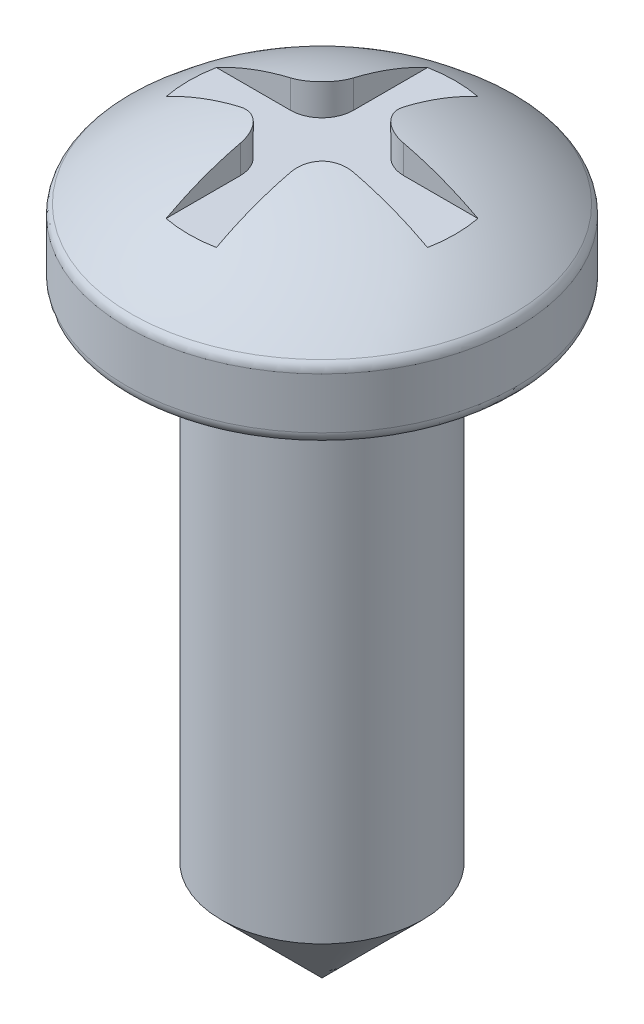
SolidWorks part; units mm, degrees
material "acero"
ref_plane "Alzado" through (0, 0, 0) normal (0, 0, 1) x (1, 0, 0)
ref_plane "Planta" through (0, 0, 0) normal (0, 1, 0) x (1, 0, 0)
ref_plane "Vista lateral" through (0, 0, 0) normal (1, 0, 0) x (0, 0, -1)
sketch "Croquis1" plane through (0, 0, 0) normal (0, 0, 1) x (1, 0, 0)
  line L0 (0, 0) -> (0, 11.9) construction
  line L1 (0, 0) -> (0, 11.9)
  line L2 (3.1, 9.7) -> (3.1, 10.5107)
  line L3 (2.9, 9.5) -> (1.6, 9.5)
  line L4 (1.6, 9.5) -> (1.6, 1.6)
  line L5 (1.6, 1.6) -> (0, 0)
  arc A0 (2.9, 9.5) -> (3.1, 9.7) centre (2.9, 9.7) ccw
  arc A1 (3.0321, 10.6608) -> (0, 11.9) centre (-0.2711, 6.9074) ccw
  arc A2 (3.1, 10.5107) -> (3.0321, 10.6608) centre (2.9, 10.5107) ccw
  point P11 (3.1, 9.5)
  point P14 (3.1, 10.6)
  dimension "D7" = 0.2
  dimension "D8" = 5
  dimension "D1" = 11.9
  dimension "D2" = 45
  dimension "D3" = 1.1
  dimension "D4" = 1.6
  dimension "D5" = 3.1
  dimension "D9" = 9.5
revolve "Revolución1" add sketch "Croquis1" angle 360 about L0
sketch "Croquis2" plane through (0, 9.5, 0) normal (0, -1, 0) x (1, 0, 0)
  line L0 (0, 0) -> (0, 3.1) construction
  line L1 (-0.4, 3.2) -> (-0.4, 0.9)
  line L2 (-0.9, 0.4) -> (-3.2, 0.4)
  line L3 (-3.2, 0.4) -> (-3.2, -0.4)
  line L4 (-3.2, -0.4) -> (-0.9, -0.4)
  line L5 (-0.4, -0.9) -> (-0.4, -3.2)
  line L6 (-0.4, -3.2) -> (0.4, -3.2)
  line L7 (0.4, -3.2) -> (0.4, -0.9)
  line L8 (0.9, -0.4) -> (3.2, -0.4)
  line L9 (3.2, -0.4) -> (3.2, 0.4)
  line L10 (3.2, 0.4) -> (0.9, 0.4)
  line L11 (0.4, 0.9) -> (0.4, 3.2)
  line L12 (0.4, 3.2) -> (-0.4, 3.2)
  circle A0 centre (0, 0) radius 3.1 construction
  arc A1 (-0.4, -0.9) -> (-0.9, -0.4) centre (-0.9, -0.9) ccw
  arc A2 (0.4, -0.9) -> (0.9, -0.4) centre (0.9, -0.9) cw
  arc A3 (0.9, 0.4) -> (0.4, 0.9) centre (0.9, 0.9) cw
  arc A4 (-0.9, 0.4) -> (-0.4, 0.9) centre (-0.9, 0.9) ccw
  point P26 (-0.4, 0.4)
  dimension "D12" = 0.5
  dimension "D1" = 0.4
  dimension "D2" = 0.8
  dimension "D3" = 3.2
  dimension "D4" = 3.2
  dimension "D5" = 3.2
  dimension "D6" = 3.2
  dimension "D7" = 0.4
  dimension "D8" = 0.4
  dimension "D9" = 0.4
  dimension "D10" = 0.4
  dimension "D11" = 0.4
extrude "Cortar-Extruir1" cut sketch "Croquis2" against normal blind 3 from offset 1.8
